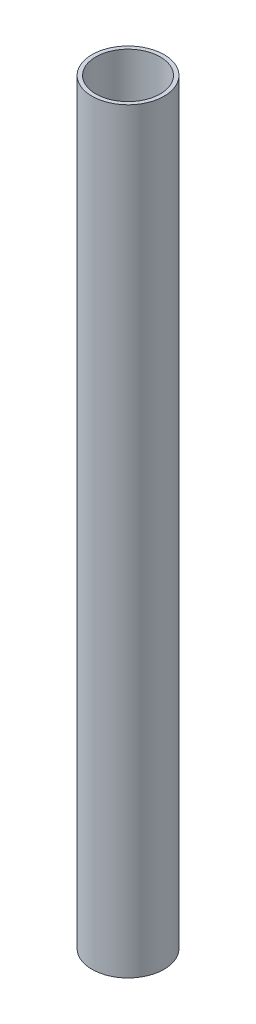
SolidWorks part; units mm, degrees
ref_plane "Front Plane" through (0, 0, 0) normal (0, 0, 1) x (1, 0, 0)
ref_plane "Top Plane" through (0, 0, 0) normal (0, 1, 0) x (1, 0, 0)
ref_plane "Right Plane" through (0, 0, 0) normal (1, 0, 0) x (0, 0, -1)
sketch "Sketch1" plane through (0, 0, 0) normal (0, 0, 1) x (1, 0, 0)
  line L0 (-3.556, 0) -> (-3.556, 74.6125)
  line L1 (-3.556, 74.6125) -> (-3.175, 74.6125)
  line L2 (-3.175, 74.6125) -> (-3.175, 0)
  line L3 (-3.175, 0) -> (-3.556, 0)
  line L4 (0, 0) -> (0, 28.6887) construction
  dimension "D1" = 3.175
  dimension "D2" = 3.556
  dimension "D3" = 74.6125
revolve "Revolve1" add sketch "Sketch1" angle 360 about L4
